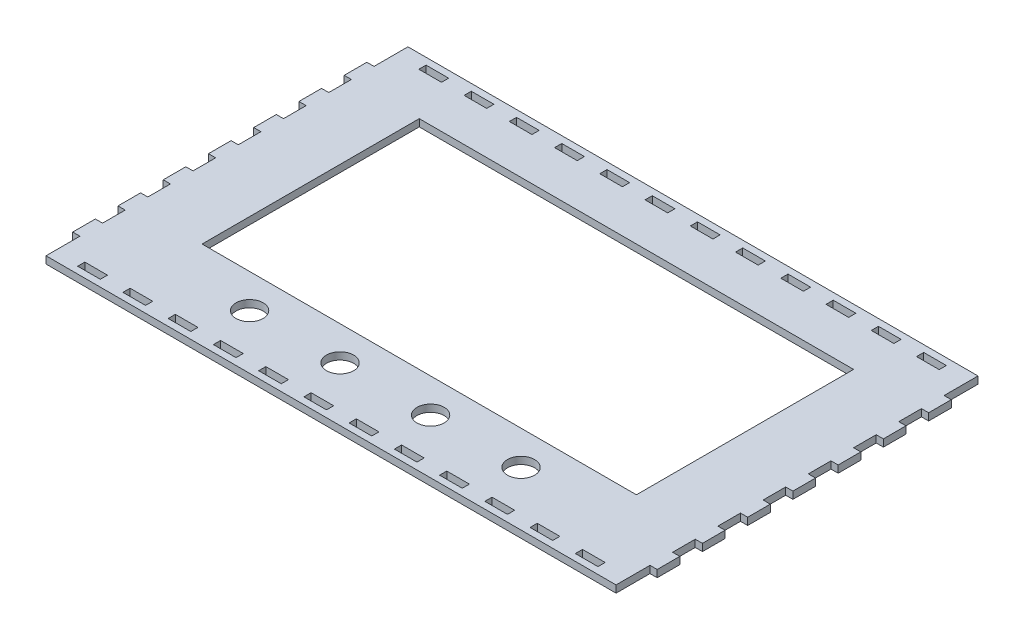
SolidWorks part; units mm, degrees
ref_plane "Front Plane" through (0, 0, 0) normal (0, 0, 1) x (1, 0, 0)
ref_plane "Top Plane" through (0, 0, 0) normal (0, 1, 0) x (1, 0, 0)
ref_plane "Right Plane" through (0, 0, 0) normal (1, 0, 0) x (0, 0, -1)
sketch "Sketch1" plane through (0, 0, 0) normal (0, 1, 0) x (1, 0, 0)
  line L0 (0, 145) -> (0, 160)
  line L1 (0, 0) -> (252, 0)
  line L2 (0, 0) -> (0, 160) construction
  line L3 (0, 160) -> (252, 160)
  line L4 (31, 157) -> (41, 157)
  line L5 (-3.175, 145) -> (0, 145)
  line L6 (-3.175, 145) -> (-3.175, 135)
  line L7 (-3.175, 135) -> (0, 135)
  line L8 (0, 115) -> (0, 105)
  line L9 (0, 125) -> (-3.175, 125)
  line L10 (0, 95) -> (0, 85)
  line L11 (0, 115) -> (-3.175, 115)
  line L12 (-3.175, 125) -> (-3.175, 115)
  line L13 (0, 105) -> (-3.175, 105)
  line L14 (0, 95) -> (0, 85)
  line L15 (0, 95) -> (-3.175, 95)
  line L16 (-3.175, 105) -> (-3.175, 95)
  line L17 (0, 85) -> (-3.175, 85)
  line L18 (-3.175, 85) -> (-3.175, 75)
  line L19 (0, 80) -> (14.6198, 80) construction
  line L20 (0, 15) -> (0, 0)
  line L21 (0, 135) -> (0, 125)
  line L22 (-3.175, 15) -> (0, 15)
  line L23 (-3.175, 25) -> (0, 25)
  line L24 (0, 35) -> (-3.175, 35)
  line L25 (0, 25) -> (0, 35)
  line L26 (0, 55) -> (-3.175, 55)
  line L27 (0, 45) -> (-3.175, 45)
  line L28 (0, 45) -> (0, 55)
  line L29 (0, 75) -> (-3.175, 75)
  line L30 (0, 65) -> (-3.175, 65)
  line L31 (0, 65) -> (0, 75)
  line L32 (-3.175, 55) -> (-3.175, 65)
  line L33 (-3.175, 35) -> (-3.175, 45)
  line L34 (-3.175, 15) -> (-3.175, 25)
  line L35 (126, 150) -> (126, -64.3384) construction
  line L36 (255.175, 15) -> (255.175, 25)
  line L37 (255.175, 35) -> (255.175, 45)
  line L38 (255.175, 55) -> (255.175, 65)
  line L39 (252, 65) -> (252, 75)
  line L40 (252, 65) -> (255.175, 65)
  line L41 (252, 75) -> (255.175, 75)
  line L42 (252, 45) -> (252, 55)
  line L43 (252, 45) -> (255.175, 45)
  line L44 (252, 55) -> (255.175, 55)
  line L45 (252, 25) -> (252, 35)
  line L46 (252, 35) -> (255.175, 35)
  line L47 (255.175, 25) -> (252, 25)
  line L48 (255.175, 15) -> (252, 15)
  line L49 (252, 135) -> (252, 125)
  line L50 (252, 15) -> (252, 0)
  line L51 (255.175, 85) -> (255.175, 75)
  line L52 (252, 85) -> (255.175, 85)
  line L53 (255.175, 105) -> (255.175, 95)
  line L54 (252, 95) -> (255.175, 95)
  line L55 (252, 95) -> (252, 85)
  line L56 (252, 105) -> (255.175, 105)
  line L57 (255.175, 125) -> (255.175, 115)
  line L58 (252, 115) -> (255.175, 115)
  line L59 (252, 95) -> (252, 85)
  line L60 (252, 125) -> (255.175, 125)
  line L61 (252, 115) -> (252, 105)
  line L62 (255.175, 135) -> (252, 135)
  line L63 (255.175, 145) -> (255.175, 135)
  line L64 (255.175, 145) -> (252, 145)
  line L65 (252, 145) -> (252, 160)
  line L66 (30, 135) -> (222, 135)
  line L67 (30, 135) -> (30, 39)
  line L68 (30, 39) -> (222, 39)
  line L69 (222, 135) -> (222, 39)
  line L70 (11, 157) -> (21, 157)
  line L71 (11, 157) -> (11, 153.825)
  line L72 (11, 153.825) -> (21, 153.825)
  line L73 (21, 157) -> (21, 153.825)
  line L74 (31, 157) -> (31, 153.825)
  line L75 (31, 153.825) -> (41, 153.825)
  line L76 (41, 157) -> (41, 153.825)
  line L77 (51, 157) -> (61, 157)
  line L78 (51, 157) -> (51, 153.825)
  line L79 (51, 153.825) -> (61, 153.825)
  line L80 (61, 157) -> (61, 153.825)
  line L81 (71, 157) -> (81, 157)
  line L82 (71, 157) -> (71, 153.825)
  line L83 (71, 153.825) -> (81, 153.825)
  line L84 (81, 157) -> (81, 153.825)
  line L85 (91, 157) -> (101, 157)
  line L86 (91, 157) -> (91, 153.825)
  line L87 (91, 153.825) -> (101, 153.825)
  line L88 (101, 157) -> (101, 153.825)
  line L89 (111, 157) -> (121, 157)
  line L90 (111, 157) -> (111, 153.825)
  line L91 (111, 153.825) -> (121, 153.825)
  line L92 (121, 157) -> (121, 153.825)
  line L93 (131, 157) -> (141, 157)
  line L94 (131, 157) -> (131, 153.825)
  line L95 (131, 153.825) -> (141, 153.825)
  line L96 (141, 157) -> (141, 153.825)
  line L97 (151, 157) -> (161, 157)
  line L98 (151, 157) -> (151, 153.825)
  line L99 (151, 153.825) -> (161, 153.825)
  line L100 (161, 157) -> (161, 153.825)
  line L101 (171, 157) -> (181, 157)
  line L102 (171, 157) -> (171, 153.825)
  line L103 (171, 153.825) -> (181, 153.825)
  line L104 (181, 157) -> (181, 153.825)
  line L105 (191, 157) -> (201, 157)
  line L106 (191, 157) -> (191, 153.825)
  line L107 (191, 153.825) -> (201, 153.825)
  line L108 (201, 157) -> (201, 153.825)
  line L109 (211, 157) -> (221, 157)
  line L110 (211, 157) -> (211, 153.825)
  line L111 (211, 153.825) -> (221, 153.825)
  line L112 (221, 157) -> (221, 153.825)
  line L113 (231, 157) -> (241, 157)
  line L114 (231, 157) -> (231, 153.825)
  line L115 (231, 153.825) -> (241, 153.825)
  line L116 (241, 157) -> (241, 153.825)
  line L117 (11, 157) -> (31, 157) construction
  line L118 (11, 3) -> (31, 3) construction
  line L119 (241, 3) -> (241, 6.175)
  line L120 (231, 6.175) -> (241, 6.175)
  line L121 (231, 3) -> (231, 6.175)
  line L122 (231, 3) -> (241, 3)
  line L123 (221, 3) -> (221, 6.175)
  line L124 (211, 6.175) -> (221, 6.175)
  line L125 (211, 3) -> (211, 6.175)
  line L126 (211, 3) -> (221, 3)
  line L127 (201, 3) -> (201, 6.175)
  line L128 (191, 6.175) -> (201, 6.175)
  line L129 (191, 3) -> (191, 6.175)
  line L130 (191, 3) -> (201, 3)
  line L131 (181, 3) -> (181, 6.175)
  line L132 (171, 6.175) -> (181, 6.175)
  line L133 (171, 3) -> (171, 6.175)
  line L134 (171, 3) -> (181, 3)
  line L135 (161, 3) -> (161, 6.175)
  line L136 (151, 6.175) -> (161, 6.175)
  line L137 (151, 3) -> (151, 6.175)
  line L138 (151, 3) -> (161, 3)
  line L139 (141, 3) -> (141, 6.175)
  line L140 (131, 6.175) -> (141, 6.175)
  line L141 (131, 3) -> (131, 6.175)
  line L142 (131, 3) -> (141, 3)
  line L143 (121, 3) -> (121, 6.175)
  line L144 (111, 6.175) -> (121, 6.175)
  line L145 (111, 3) -> (111, 6.175)
  line L146 (111, 3) -> (121, 3)
  line L147 (101, 3) -> (101, 6.175)
  line L148 (91, 6.175) -> (101, 6.175)
  line L149 (91, 3) -> (91, 6.175)
  line L150 (91, 3) -> (101, 3)
  line L151 (81, 3) -> (81, 6.175)
  line L152 (71, 6.175) -> (81, 6.175)
  line L153 (71, 3) -> (71, 6.175)
  line L154 (71, 3) -> (81, 3)
  line L155 (61, 3) -> (61, 6.175)
  line L156 (51, 6.175) -> (61, 6.175)
  line L157 (51, 3) -> (51, 6.175)
  line L158 (51, 3) -> (61, 3)
  line L159 (41, 3) -> (41, 6.175)
  line L160 (31, 6.175) -> (41, 6.175)
  line L161 (31, 3) -> (31, 6.175)
  line L162 (21, 3) -> (21, 6.175)
  line L163 (11, 6.175) -> (21, 6.175)
  line L164 (11, 3) -> (11, 6.175)
  line L165 (11, 3) -> (21, 3)
  line L166 (31, 3) -> (41, 3)
  circle A0 centre (106, 24) radius 6
  circle A1 centre (66, 24) radius 6
  circle A2 centre (186, 24) radius 6
  circle A3 centre (146, 24) radius 6
  point P9 (-1.5875, 145)
  point P18 (-1.5875, 105)
  point P38 (-3.175, 80)
  point P68 (255.175, 80)
  dimension "D19" = 20
  dimension "D20" = 40
  dimension "D21" = 15
  dimension "D22" = 15
  dimension "D2" = 252
  dimension "D3" = 3.175
  dimension "D4" = 10
  dimension "D5" = 15
  dimension "D6" = 10
  dimension "D7" = 3.175
  dimension "D8" = 10
  dimension "D9" = 10
  dimension "D10" = 3.175
  dimension "D11" = 10
  dimension "D12" = 3.175
  dimension "D13" = 10
  dimension "D14" = 5
  dimension "D15" = 192
  dimension "D16" = 30
  dimension "D17" = 96
  dimension "D18" = 25
  dimension "D23" = 10
  dimension "D24" = 3.175
  dimension "D25" = 11
  dimension "D26" = 3
  dimension "D28" = 20
  dimension "D29" = 11
  dimension "D27" = 12
extrude "Boss-Extrude1" add sketch "Sketch1" along normal blind 3.175 contours L64 L65 L3 L0 L5 L6 L7 L21 L9 L12 L11 L8 L13 L16 L15 L10 L17 L18 L29 L31 L30 L32 L26 L28 L27 L33 L24 L25 L23 L34 L22 L20 L1 L50 L48 L36 L47 L45 L46 L37 L43 L42 L44 L38 L40 L39 L41 L51 L52 L55 L54
